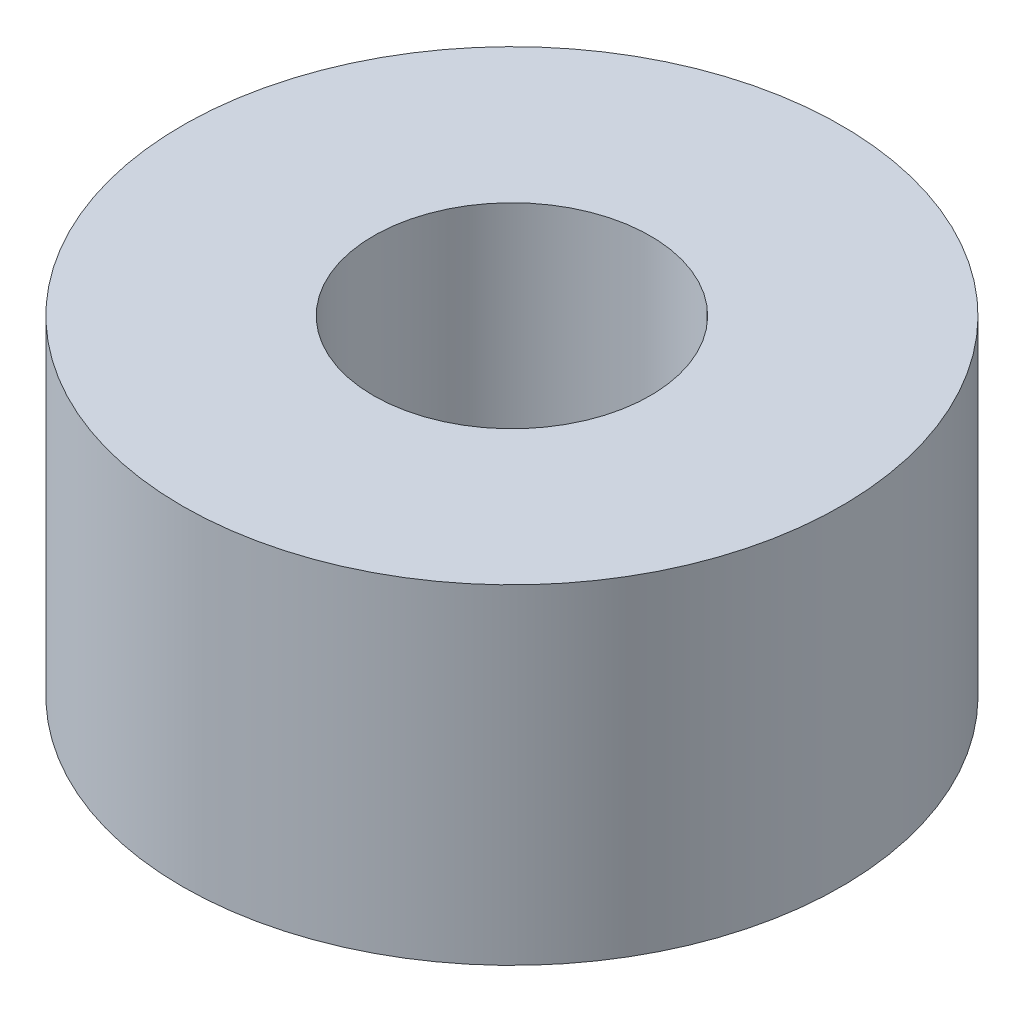
SolidWorks part; units mm, degrees
material "Plain Carbon Steel"
ref_plane "Front Plane" through (0, 0, 0) normal (0, 0, 1) x (1, 0, 0)
ref_plane "Top Plane" through (0, 0, 0) normal (0, 1, 0) x (1, 0, 0)
ref_plane "Right Plane" through (0, 0, 0) normal (1, 0, 0) x (0, 0, -1)
sketch "Sketch1" plane through (0, 0, 0) normal (0, 0, 1) x (1, 0, 0)
  line L0 (0, 4.7625) -> (0, -4.7625) construction
  line L1 (4.0005, 4.7625) -> (9.525, 4.7625)
  line L2 (4.0005, 4.7625) -> (4.0005, -4.7625)
  line L3 (4.0005, -4.7625) -> (9.525, -4.7625)
  line L4 (9.525, 4.7625) -> (9.525, -4.7625)
  line L5 (0, 0) -> (4.0005, 0) construction
  dimension "D1" = 9.525
  dimension "D2" = 8.001
  dimension "D3" = 19.05
revolve "Revolve1" add sketch "Sketch1" angle 360 about L0
